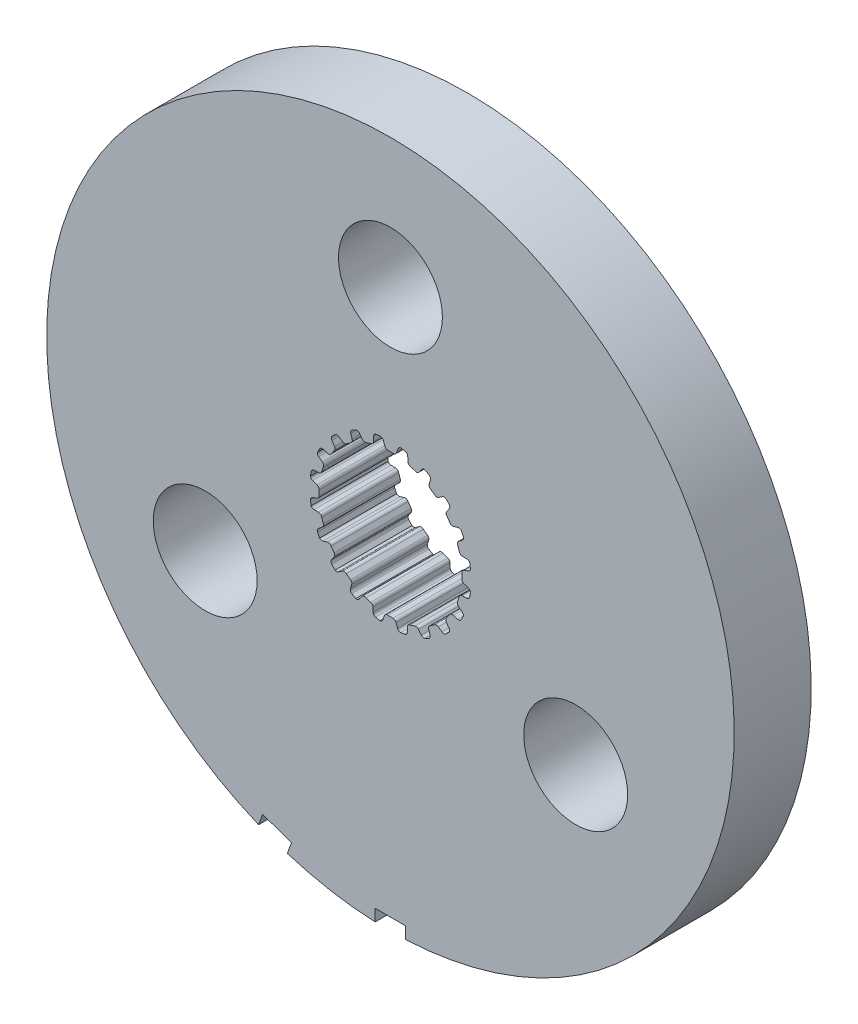
SolidWorks part; units mm, degrees
ref_plane "Front Plane" through (0, 0, 0) normal (0, 0, 1) x (1, 0, 0)
ref_plane "Top Plane" through (0, 0, 0) normal (0, 1, 0) x (1, 0, 0)
ref_plane "Right Plane" through (0, 0, 0) normal (1, 0, 0) x (0, 0, -1)
sketch "Sketch1" plane through (0, 0, 0) normal (0, 0, 1) x (1, 0, 0)
  line L0 (-0.1069, 2.9699) -> (0.1069, 2.9699)
  line L1 (0.3159, 3.2375) -> (0.2537, 3.0575)
  line L2 (-0.2964, 3.2367) -> (-0.2318, 3.0575)
  line L3 (-0.2964, 3.2367) -> (0.3159, 3.2375) construction
  line L4 (0, 3.3252) -> (0, 0) construction
  line L5 (-0.2318, 3.0575) -> (0.2537, 3.0575) construction
  line L6 (-0.4281, 3.3241) -> (0.4281, 3.3263) construction
  line L7 (0.7183, 3.1698) -> (0.7244, 2.9795)
  line L8 (0.816, 2.8576) -> (1.0195, 2.7915)
  line L9 (1.3009, 2.9815) -> (1.1862, 2.8295)
  line L10 (1.6627, 2.7927) -> (1.6097, 2.6099)
  line L11 (1.6591, 2.4655) -> (1.8322, 2.3398)
  line L12 (2.1585, 2.4335) -> (2.0025, 2.3245)
  line L13 (2.4443, 2.1423) -> (2.3374, 1.9847)
  line L14 (2.3398, 1.8322) -> (2.4655, 1.6591)
  line L15 (2.8049, 1.6474) -> (2.6228, 1.5919)
  line L16 (2.9866, 1.2821) -> (2.8363, 1.1653)
  line L17 (2.7915, 1.0195) -> (2.8576, 0.816)
  line L18 (3.1767, 0.7) -> (2.9863, 0.7035)
  line L19 (3.2367, 0.2964) -> (3.0575, 0.2318)
  line L20 (2.9699, 0.1069) -> (2.9699, -0.1069)
  line L21 (3.2375, -0.3159) -> (3.0575, -0.2537)
  line L22 (3.1698, -0.7183) -> (2.9795, -0.7244)
  line L23 (2.8576, -0.816) -> (2.7915, -1.0195)
  line L24 (2.9815, -1.3009) -> (2.8295, -1.1862)
  line L25 (2.7927, -1.6627) -> (2.6099, -1.6097)
  line L26 (2.4655, -1.6591) -> (2.3398, -1.8322)
  line L27 (2.4335, -2.1585) -> (2.3245, -2.0025)
  line L28 (2.1423, -2.4443) -> (1.9847, -2.3374)
  line L29 (1.8322, -2.3398) -> (1.6591, -2.4655)
  line L30 (1.6474, -2.8049) -> (1.5919, -2.6228)
  line L31 (1.2821, -2.9866) -> (1.1653, -2.8363)
  line L32 (1.0195, -2.7915) -> (0.816, -2.8576)
  line L33 (0.7, -3.1767) -> (0.7035, -2.9863)
  line L34 (0.2964, -3.2367) -> (0.2318, -3.0575)
  line L35 (0.1069, -2.9699) -> (-0.1069, -2.9699)
  line L36 (-0.3159, -3.2375) -> (-0.2537, -3.0575)
  line L37 (-0.7183, -3.1698) -> (-0.7244, -2.9795)
  line L38 (-0.816, -2.8576) -> (-1.0195, -2.7915)
  line L39 (-1.3009, -2.9815) -> (-1.1862, -2.8295)
  line L40 (-1.6627, -2.7927) -> (-1.6097, -2.6099)
  line L41 (-1.6591, -2.4655) -> (-1.8322, -2.3398)
  line L42 (-2.1585, -2.4335) -> (-2.0025, -2.3245)
  line L43 (-2.4443, -2.1423) -> (-2.3374, -1.9847)
  line L44 (-2.3398, -1.8322) -> (-2.4655, -1.6591)
  line L45 (-2.8049, -1.6474) -> (-2.6228, -1.5919)
  line L46 (-2.9866, -1.2821) -> (-2.8363, -1.1653)
  line L47 (-2.7915, -1.0195) -> (-2.8576, -0.816)
  line L48 (-3.1767, -0.7) -> (-2.9863, -0.7035)
  line L49 (-3.2367, -0.2964) -> (-3.0575, -0.2318)
  line L50 (-2.9699, -0.1069) -> (-2.9699, 0.1069)
  line L51 (-3.2375, 0.3159) -> (-3.0575, 0.2537)
  line L52 (-3.1698, 0.7183) -> (-2.9795, 0.7244)
  line L53 (-2.8576, 0.816) -> (-2.7915, 1.0195)
  line L54 (-2.9815, 1.3009) -> (-2.8295, 1.1862)
  line L55 (-2.7927, 1.6627) -> (-2.6099, 1.6097)
  line L56 (-2.4655, 1.6591) -> (-2.3398, 1.8322)
  line L57 (-2.4335, 2.1585) -> (-2.3245, 2.0025)
  line L58 (-2.1423, 2.4443) -> (-1.9847, 2.3374)
  line L59 (-1.8322, 2.3398) -> (-1.6591, 2.4655)
  line L60 (-1.6474, 2.8049) -> (-1.5919, 2.6228)
  line L61 (-1.2821, 2.9866) -> (-1.1653, 2.8363)
  line L62 (-1.0195, 2.7915) -> (-0.816, 2.8576)
  line L63 (-0.7, 3.1767) -> (-0.7035, 2.9863)
  line L64 (0.4281, 3.3263) -> (0.62, 3.2938)
  line L65 (1.4351, 3.0312) -> (1.6075, 2.9409)
  line L66 (2.3015, 2.4394) -> (2.4376, 2.3003)
  line L67 (2.9427, 1.6088) -> (3.0291, 1.4344)
  line L68 (3.2958, 0.6207) -> (3.3241, 0.4281)
  line L69 (3.3263, -0.4281) -> (3.2938, -0.62)
  line L70 (3.0312, -1.4351) -> (2.9409, -1.6075)
  line L71 (2.4394, -2.3015) -> (2.3003, -2.4376)
  line L72 (1.6088, -2.9427) -> (1.4344, -3.0291)
  line L73 (0.6207, -3.2958) -> (0.4281, -3.3241)
  line L74 (-0.4281, -3.3263) -> (-0.62, -3.2938)
  line L75 (-1.4351, -3.0312) -> (-1.6075, -2.9409)
  line L76 (-2.3015, -2.4394) -> (-2.4376, -2.3003)
  line L77 (-2.9427, -1.6088) -> (-3.0291, -1.4344)
  line L78 (-3.2958, -0.6207) -> (-3.3241, -0.4281)
  line L79 (-3.3263, 0.4281) -> (-3.2938, 0.62)
  line L80 (-3.0312, 1.4351) -> (-2.9409, 1.6075)
  line L81 (-2.4394, 2.3015) -> (-2.3003, 2.4376)
  line L82 (-1.6088, 2.9427) -> (-1.4344, 3.0291)
  line L83 (-0.6207, 3.2958) -> (-0.4281, 3.3241)
  arc A0 (0.2537, 3.0575) -> (0.1069, 2.9699) centre (0.1283, 3.1009) cw
  arc A1 (-0.2318, 3.0575) -> (-0.1069, 2.9699) centre (-0.1069, 3.1026) ccw
  arc A2 (0.62, 3.2938) -> (0.7183, 3.1698) centre (0.5856, 3.1656) cw
  arc A3 (0.7244, 2.9795) -> (0.816, 2.8576) centre (0.857, 2.9838) ccw
  arc A4 (-0.4281, 3.3241) -> (-0.2964, 3.2367) centre (-0.4213, 3.1916) cw
  arc A5 (0.4281, 3.3263) -> (0.3159, 3.2375) centre (0.4413, 3.1942) ccw
  arc A6 (1.1862, 2.8295) -> (1.0195, 2.7915) centre (1.0802, 2.9095) cw
  arc A7 (1.4351, 3.0312) -> (1.3009, 2.9815) centre (1.4068, 2.9015) ccw
  arc A8 (1.6075, 2.9409) -> (1.6627, 2.7927) centre (1.5352, 2.8297) cw
  arc A9 (1.6097, 2.6099) -> (1.6591, 2.4655) centre (1.7371, 2.5729) ccw
  arc A10 (2.0025, 2.3245) -> (1.8322, 2.3398) centre (1.9264, 2.4332) cw
  arc A11 (2.3015, 2.4394) -> (2.1585, 2.4335) centre (2.2346, 2.3248) ccw
  arc A12 (2.4376, 2.3003) -> (2.4443, 2.1423) centre (2.3345, 2.2168) cw
  arc A13 (2.3374, 1.9847) -> (2.3398, 1.8322) centre (2.4472, 1.9102) ccw
  arc A14 (2.6228, 1.5919) -> (2.4655, 1.6591) centre (2.5841, 1.7189) cw
  arc A15 (2.9427, 1.6088) -> (2.8049, 1.6474) centre (2.8436, 1.5205) ccw
  arc A16 (3.0291, 1.4344) -> (2.9866, 1.2821) centre (2.9052, 1.3869) cw
  arc A17 (2.8363, 1.1653) -> (2.7915, 1.0195) centre (2.9177, 1.0605) ccw
  arc A18 (2.9863, 0.7035) -> (2.8576, 0.816) centre (2.9887, 0.8362) cw
  arc A19 (3.2958, 0.6207) -> (3.1767, 0.7) centre (3.1743, 0.5673) ccw
  arc A20 (3.3241, 0.4281) -> (3.2367, 0.2964) centre (3.1916, 0.4213) cw
  arc A21 (3.0575, 0.2318) -> (2.9699, 0.1069) centre (3.1026, 0.1069) ccw
  arc A22 (3.0575, -0.2537) -> (2.9699, -0.1069) centre (3.1009, -0.1283) cw
  arc A23 (3.3263, -0.4281) -> (3.2375, -0.3159) centre (3.1942, -0.4413) ccw
  arc A24 (3.2938, -0.62) -> (3.1698, -0.7183) centre (3.1656, -0.5856) cw
  arc A25 (2.9795, -0.7244) -> (2.8576, -0.816) centre (2.9838, -0.857) ccw
  arc A26 (2.8295, -1.1862) -> (2.7915, -1.0195) centre (2.9095, -1.0802) cw
  arc A27 (3.0312, -1.4351) -> (2.9815, -1.3009) centre (2.9015, -1.4068) ccw
  arc A28 (2.9409, -1.6075) -> (2.7927, -1.6627) centre (2.8297, -1.5352) cw
  arc A29 (2.6099, -1.6097) -> (2.4655, -1.6591) centre (2.5729, -1.7371) ccw
  arc A30 (2.3245, -2.0025) -> (2.3398, -1.8322) centre (2.4332, -1.9264) cw
  arc A31 (2.4394, -2.3015) -> (2.4335, -2.1585) centre (2.3248, -2.2346) ccw
  arc A32 (2.3003, -2.4376) -> (2.1423, -2.4443) centre (2.2168, -2.3345) cw
  arc A33 (1.9847, -2.3374) -> (1.8322, -2.3398) centre (1.9102, -2.4472) ccw
  arc A34 (1.5919, -2.6228) -> (1.6591, -2.4655) centre (1.7189, -2.5841) cw
  arc A35 (1.6088, -2.9427) -> (1.6474, -2.8049) centre (1.5205, -2.8436) ccw
  arc A36 (1.4344, -3.0291) -> (1.2821, -2.9866) centre (1.3869, -2.9052) cw
  arc A37 (1.1653, -2.8363) -> (1.0195, -2.7915) centre (1.0605, -2.9177) ccw
  arc A38 (0.7035, -2.9863) -> (0.816, -2.8576) centre (0.8362, -2.9887) cw
  arc A39 (0.6207, -3.2958) -> (0.7, -3.1767) centre (0.5673, -3.1743) ccw
  arc A40 (0.4281, -3.3241) -> (0.2964, -3.2367) centre (0.4213, -3.1916) cw
  arc A41 (0.2318, -3.0575) -> (0.1069, -2.9699) centre (0.1069, -3.1026) ccw
  arc A42 (-0.2537, -3.0575) -> (-0.1069, -2.9699) centre (-0.1283, -3.1009) cw
  arc A43 (-0.4281, -3.3263) -> (-0.3159, -3.2375) centre (-0.4413, -3.1942) ccw
  arc A44 (-0.62, -3.2938) -> (-0.7183, -3.1698) centre (-0.5856, -3.1656) cw
  arc A45 (-0.7244, -2.9795) -> (-0.816, -2.8576) centre (-0.857, -2.9838) ccw
  arc A46 (-1.1862, -2.8295) -> (-1.0195, -2.7915) centre (-1.0802, -2.9095) cw
  arc A47 (-1.4351, -3.0312) -> (-1.3009, -2.9815) centre (-1.4068, -2.9015) ccw
  arc A48 (-1.6075, -2.9409) -> (-1.6627, -2.7927) centre (-1.5352, -2.8297) cw
  arc A49 (-1.6097, -2.6099) -> (-1.6591, -2.4655) centre (-1.7371, -2.5729) ccw
  arc A50 (-2.0025, -2.3245) -> (-1.8322, -2.3398) centre (-1.9264, -2.4332) cw
  arc A51 (-2.3015, -2.4394) -> (-2.1585, -2.4335) centre (-2.2346, -2.3248) ccw
  arc A52 (-2.4376, -2.3003) -> (-2.4443, -2.1423) centre (-2.3345, -2.2168) cw
  arc A53 (-2.3374, -1.9847) -> (-2.3398, -1.8322) centre (-2.4472, -1.9102) ccw
  arc A54 (-2.6228, -1.5919) -> (-2.4655, -1.6591) centre (-2.5841, -1.7189) cw
  arc A55 (-2.9427, -1.6088) -> (-2.8049, -1.6474) centre (-2.8436, -1.5205) ccw
  arc A56 (-3.0291, -1.4344) -> (-2.9866, -1.2821) centre (-2.9052, -1.3869) cw
  arc A57 (-2.8363, -1.1653) -> (-2.7915, -1.0195) centre (-2.9177, -1.0605) ccw
  arc A58 (-2.9863, -0.7035) -> (-2.8576, -0.816) centre (-2.9887, -0.8362) cw
  arc A59 (-3.2958, -0.6207) -> (-3.1767, -0.7) centre (-3.1743, -0.5673) ccw
  arc A60 (-3.3241, -0.4281) -> (-3.2367, -0.2964) centre (-3.1916, -0.4213) cw
  arc A61 (-3.0575, -0.2318) -> (-2.9699, -0.1069) centre (-3.1026, -0.1069) ccw
  arc A62 (-3.0575, 0.2537) -> (-2.9699, 0.1069) centre (-3.1009, 0.1283) cw
  arc A63 (-3.3263, 0.4281) -> (-3.2375, 0.3159) centre (-3.1942, 0.4413) ccw
  arc A64 (-3.2938, 0.62) -> (-3.1698, 0.7183) centre (-3.1656, 0.5856) cw
  arc A65 (-2.9795, 0.7244) -> (-2.8576, 0.816) centre (-2.9838, 0.857) ccw
  arc A66 (-2.8295, 1.1862) -> (-2.7915, 1.0195) centre (-2.9095, 1.0802) cw
  arc A67 (-3.0312, 1.4351) -> (-2.9815, 1.3009) centre (-2.9015, 1.4068) ccw
  arc A68 (-2.9409, 1.6075) -> (-2.7927, 1.6627) centre (-2.8297, 1.5352) cw
  arc A69 (-2.6099, 1.6097) -> (-2.4655, 1.6591) centre (-2.5729, 1.7371) ccw
  arc A70 (-2.3245, 2.0025) -> (-2.3398, 1.8322) centre (-2.4332, 1.9264) cw
  arc A71 (-2.4394, 2.3015) -> (-2.4335, 2.1585) centre (-2.3248, 2.2346) ccw
  arc A72 (-2.3003, 2.4376) -> (-2.1423, 2.4443) centre (-2.2168, 2.3345) cw
  arc A73 (-1.9847, 2.3374) -> (-1.8322, 2.3398) centre (-1.9102, 2.4472) ccw
  arc A74 (-1.5919, 2.6228) -> (-1.6591, 2.4655) centre (-1.7189, 2.5841) cw
  arc A75 (-1.6088, 2.9427) -> (-1.6474, 2.8049) centre (-1.5205, 2.8436) ccw
  arc A76 (-1.4344, 3.0291) -> (-1.2821, 2.9866) centre (-1.3869, 2.9052) cw
  arc A77 (-1.1653, 2.8363) -> (-1.0195, 2.7915) centre (-1.0605, 2.9177) ccw
  arc A78 (-0.7035, 2.9863) -> (-0.816, 2.8576) centre (-0.8362, 2.9887) cw
  arc A79 (-0.6207, 3.2958) -> (-0.7, 3.1767) centre (-0.5673, 3.1743) ccw
  circle A80 centre (0, 0) radius 14.2875
  point P14 (0, 2.9699)
  point P247 (0, 0)
  dimension "D4" = 0.1327
  dimension "D8" = 20
  dimension "D9" = 28.575
  dimension "D1" = 2.9699
  dimension "D2" = 0.2139
  dimension "D3" = 0.1904
  dimension "D5" = 0.0877
  dimension "D6" = 0.4855
  dimension "D7" = 0.8563
extrude "Boss-Extrude1" add sketch "Sketch1" along normal blind 3.2004
sketch "Sketch5" plane through (0, 0, 3.2004) normal (0, 0, 1) x (1, 0, 0)
  line L0 (0, 8.89) -> (0, 0) construction
  line L1 (0, 3.3252) -> (0, 0) construction
  circle A0 centre (0, 0) radius 14.2875 construction
  circle A1 centre (0, 8.89) radius 2.159
  circle A2 centre (7.699, -4.445) radius 2.159
  circle A3 centre (-7.699, -4.445) radius 2.159
  point P15 (0, 0)
  dimension "D2" = 4.318
  dimension "D1" = 8.89
  dimension "D3" = 3
extrude "Cut-Extrude2" cut sketch "Sketch5" against normal up to surface (3.2004 mm away) up to face at (14.2875, 0, 0)
sketch "Sketch7" plane through (0, 0, 3.2004) normal (0, 0, 1) x (1, 0, 0)
  line L0 (-4.8866, -13.4259) -> (0, 0) construction
  line L1 (-4.2899, -13.643) -> (-4.1162, -13.1657)
  line L2 (-4.1162, -13.1657) -> (-5.3096, -12.7313)
  line L3 (-5.3096, -12.7313) -> (-5.4833, -13.2087)
  line L4 (-5.4833, -13.2087) -> (-4.2899, -13.643)
  line L6 (0, -14.2875) -> (0, 0) construction
  line L7 (0.635, -14.2875) -> (0.635, -13.7795)
  line L8 (0.635, -13.7795) -> (-0.635, -13.7795)
  line L9 (-0.635, -13.7795) -> (-0.635, -14.2875)
  line L10 (-0.635, -14.2875) -> (0.635, -14.2875)
  line L11 (0, 3.3252) -> (0, 0) construction
  circle A0 centre (0, 0) radius 14.2875 construction
  circle A3 centre (0, 0) radius 14.2875 construction
  circle A4 centre (0, 0) radius 14.2875 construction
  point P20 (0, 0)
  dimension "D1" = 1.27
  dimension "D2" = 0.508
  dimension "D3" = 20
extrude "Cut-Extrude3" cut sketch "Sketch7" against normal up to surface (3.2004 mm away) up to face at (2.159, 8.89, 0)
